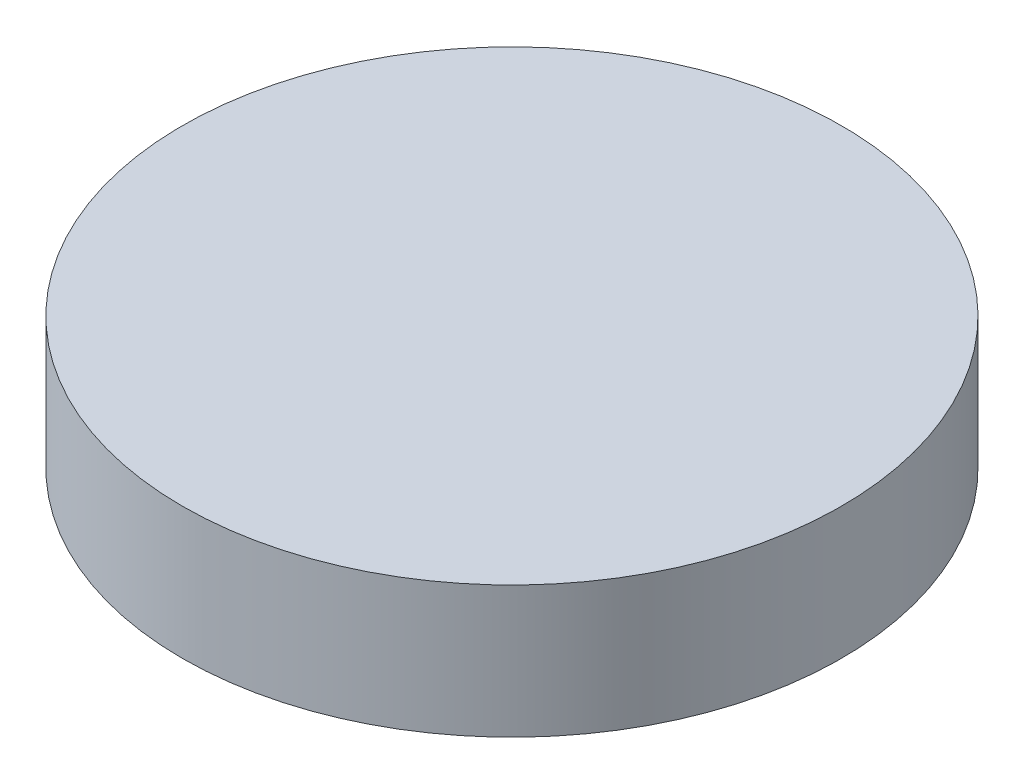
SolidWorks part; units mm, degrees
ref_plane "Front Plane" through (0, 0, 0) normal (0, 0, 1) x (1, 0, 0)
ref_plane "Top Plane" through (0, 0, 0) normal (0, 1, 0) x (1, 0, 0)
ref_plane "Right Plane" through (0, 0, 0) normal (1, 0, 0) x (0, 0, -1)
sketch "Sketch1" plane through (0, 0, 0) normal (0, 1, 0) x (1, 0, 0)
  circle A0 centre (0, 0) radius 2.5
  dimension "D1" = 5
extrude "Boss-Extrude1" add sketch "Sketch1" along normal blind 1
